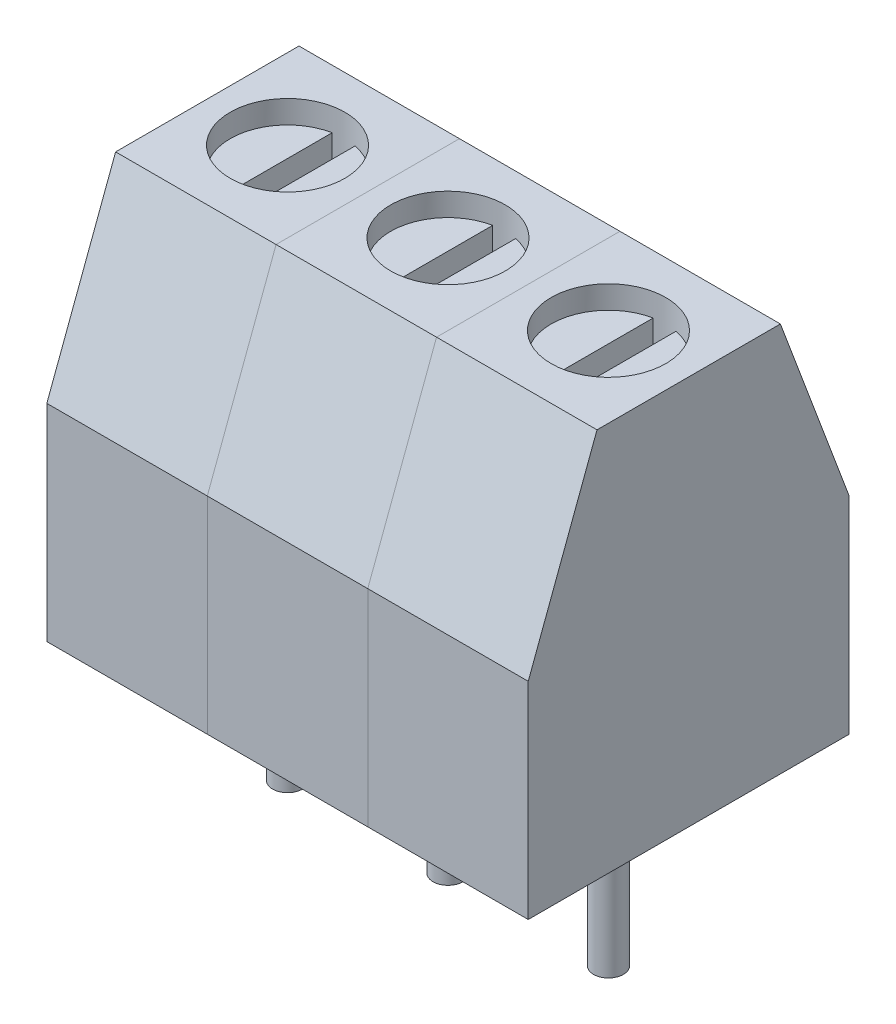
SolidWorks part; units mm, degrees
ref_plane "정면" through (0, 0, 0) normal (0, 0, 1) x (1, 0, 0)
ref_plane "윗면" through (0, 0, 0) normal (0, 1, 0) x (1, 0, 0)
ref_plane "우측면" through (0, 0, 0) normal (1, 0, 0) x (0, 0, -1)
sketch "스케치1" plane through (0, 0, 0) normal (1, 0, 0) x (0, 0, -1)
  line L0 (0, 4.5) -> (0, 8.5) construction
  line L1 (0, 0) -> (7, 0)
  line L2 (0, 0) -> (0, 4.5)
  line L3 (0, 8.5) -> (7, 8.5) construction
  line L4 (7, 0) -> (7, 4.5)
  line L5 (1.5, 8.5) -> (5.5, 8.5)
  line L6 (1.5, 8.5) -> (0, 4.5)
  line L7 (5.5, 8.5) -> (7, 4.5)
  line L8 (7, 4.5) -> (7, 8.5) construction
  line L9 (0, 4.5) -> (7, 4.5) construction
  point P10 (3.5, 8.5)
  dimension "D1" = 4
  dimension "D2" = 7
  dimension "D3" = 8.5
  dimension "D4" = 4.5
extrude "보스-돌출1" add sketch "스케치1" along normal blind 3.5
sketch "스케치3" plane through (0, 0, -7) normal (0, 0, -1) x (-1, 0, 0)
  line L0 (-3.5, 4.5) -> (0, 4.5) construction
  line L1 (-3.25, 0.5) -> (-0.25, 0.5)
  line L2 (-3.25, 0.5) -> (-3.25, 4.5)
  line L3 (-3.25, 4.5) -> (-0.25, 4.5)
  line L4 (-0.25, 0.5) -> (-0.25, 4.5)
  line L5 (-3.5, 0) -> (-3.5, 4.5) construction
  line L6 (0, 0) -> (0, 4.5) construction
  line L7 (-3.5, 0) -> (0, 0) construction
  dimension "D1" = 0.25
  dimension "D2" = 0.25
  dimension "D3" = 0.5
extrude "컷-돌출1" cut sketch "스케치3" against normal blind 1.5
sketch "스케치4" plane through (0, 8.5, 0) normal (0, 1, 0) x (1, 0, 0)
  circle A0 centre (1.75, 3.5) radius 1.25
extrude "컷-돌출2" cut sketch "스케치4" against normal blind 0.5
sketch "스케치5" plane through (0, 8, 0) normal (0, 1, 0) x (1, 0, 0)
  line L2 (1.5001, 4.7248) -> (1.5001, 2.2752)
  line L4 (1.9999, 4.7248) -> (1.9999, 2.2752)
  line L5 (1.5001, 4.7248) -> (1.9999, 2.2752) construction
  line L6 (1.5001, 2.2752) -> (1.9999, 4.7248) construction
  arc A0 (1.5001, 2.2752) -> (1.9999, 2.2752) centre (1.75, 3.5) ccw
  circle A1 centre (1.75, 3.5) radius 1.25
  arc A2 (1.9999, 4.7248) -> (1.5001, 4.7248) centre (1.75, 3.5) ccw
  dimension "D1" = 0
extrude "컷-돌출3" cut sketch "스케치5" against normal blind 0.5
sketch "스케치7" plane through (0, 0, -5.5) normal (0, 0, -1) x (-1, 0, 0)
  line L0 (-3.25, 4.5) -> (-3.25, 0.5) construction
  line L1 (-3.25, 0.5) -> (-0.25, 0.5) construction
  circle A0 centre (-1.75, 2) radius 1
  dimension "D1" = 1.5
  dimension "D2" = 2
  dimension "D3" = 1.5
extrude "컷-돌출4" cut sketch "스케치7" against normal blind 3
pattern_linear "선형 패턴1" [suppressed] count 3 spacing 3.5
sketch "Sketch1" plane through (0, 0, 0) normal (0, -1, 0) x (1, 0, 0)
  line L4 (0, 0) -> (0, -7)
  line L5 (0, -7) -> (3.5, -7)
  line L6 (3.5, -7) -> (3.5, 0)
  line L7 (3.5, 0) -> (0, 0)
  line L8 (0, 0) -> (0, -7)
  line L9 (0, -7) -> (3.5, -7)
  line L10 (3.5, -7) -> (3.5, 0)
  line L11 (3.5, 0) -> (0, 0)
  circle A0 centre (1.75, -3.5) radius 0.325
  dimension "D2" = 1.75
  dimension "D3" = 3.5
  dimension "D4" = 7
  dimension "D5" = 3.5
  dimension "D1" = 0
extrude "Boss-Extrude1" add sketch "Sketch1" along normal blind 3.5 contours A0
pattern_linear "LPattern1" count 3 spacing 3.5 along (1, 0, 0) of bodies 108
